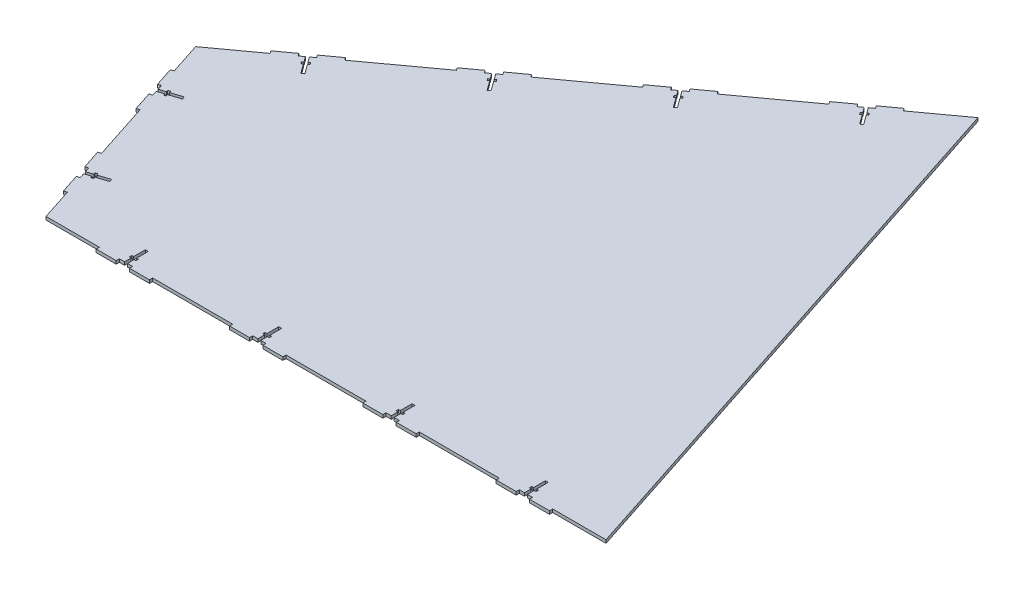
SolidWorks part; units mm, degrees
ref_plane "Front Plane" through (0, 0, 0) normal (0, 0, 1) x (1, 0, 0)
ref_plane "Top Plane" through (0, 0, 0) normal (0, 1, 0) x (1, 0, 0)
ref_plane "Right Plane" through (0, 0, 0) normal (1, 0, 0) x (0, 0, -1)
sketch "Sketch5" plane through (0, 0, 0) normal (0, 1, 0) x (1, 0, 0)
  line L0 (0, 0) -> (533.4, 0)
  line L1 (533.4, 0) -> (362.4036, 525.3201)
  line L2 (362.4036, 525.3201) -> (-68.7917, 211.3357)
  line L3 (-68.7917, 211.3357) -> (0, 0)
  line L4 (-68.7917, 211.3357) -> (413.506, 368.3279) construction
  line L5 (0, 0) -> (482.2976, 156.9922) construction
  dimension "D1" = 222.25
  dimension "D2" = 165.1
  dimension "D3" = 165.1
  dimension "D4" = 533.4
extrude "Boss-Extrude1" add sketch "Sketch5" along normal blind 3
sketch "Sketch6" plane through (0, 3, 0) normal (0, 1, 0) x (1, 0, 0)
  line L0 (74.8284, 0) -> (77.5716, 0)
  line L1 (76.2, 19.86) -> (76.2, 0) construction
  line L2 (204.5716, 19.86) -> (204.5716, 8.636)
  line L3 (201.8284, 19.86) -> (204.5716, 19.86)
  line L4 (201.8284, 8.636) -> (201.8284, 19.86)
  line L5 (299.6955, 479.6578) -> (301.913, 481.2726)
  line L6 (0, 0) -> (533.4, 0) construction
  line L7 (74.8284, 0) -> (74.8284, 6.35)
  line L8 (74.8284, 6.35) -> (73.0504, 6.35)
  line L9 (73.0504, 6.35) -> (73.0504, 8.636)
  line L10 (73.0504, 8.636) -> (74.8284, 8.636)
  line L11 (74.8284, 8.636) -> (74.8284, 19.86)
  line L12 (74.8284, 19.86) -> (77.5716, 19.86)
  line L13 (77.5716, 19.86) -> (77.5716, 8.636)
  line L14 (77.5716, 8.636) -> (79.3496, 8.636)
  line L15 (79.3496, 8.636) -> (79.3496, 6.35)
  line L16 (79.3496, 6.35) -> (77.5716, 6.35)
  line L17 (77.5716, 6.35) -> (77.5716, 0)
  line L18 (200.0504, 8.636) -> (201.8284, 8.636)
  line L19 (200.0504, 6.35) -> (200.0504, 8.636)
  line L20 (201.8284, 6.35) -> (200.0504, 6.35)
  line L21 (201.8284, 0) -> (201.8284, 6.35)
  line L22 (204.5716, 6.35) -> (204.5716, 0)
  line L23 (206.3496, 6.35) -> (204.5716, 6.35)
  line L24 (206.3496, 8.636) -> (206.3496, 6.35)
  line L25 (204.5716, 8.636) -> (206.3496, 8.636)
  line L26 (201.8284, 0) -> (204.5716, 0)
  line L27 (331.5716, 19.86) -> (331.5716, 8.636)
  line L28 (328.8284, 19.86) -> (331.5716, 19.86)
  line L29 (328.8284, 8.636) -> (328.8284, 19.86)
  line L30 (327.0504, 8.636) -> (328.8284, 8.636)
  line L31 (327.0504, 6.35) -> (327.0504, 8.636)
  line L32 (328.8284, 6.35) -> (327.0504, 6.35)
  line L33 (328.8284, 0) -> (328.8284, 6.35)
  line L34 (331.5716, 6.35) -> (331.5716, 0)
  line L35 (333.3496, 6.35) -> (331.5716, 6.35)
  line L36 (333.3496, 8.636) -> (333.3496, 6.35)
  line L37 (331.5716, 8.636) -> (333.3496, 8.636)
  line L38 (328.8284, 0) -> (331.5716, 0)
  line L39 (458.5716, 19.86) -> (458.5716, 8.636)
  line L40 (455.8284, 19.86) -> (458.5716, 19.86)
  line L41 (455.8284, 8.636) -> (455.8284, 19.86)
  line L42 (454.0504, 8.636) -> (455.8284, 8.636)
  line L43 (454.0504, 6.35) -> (454.0504, 8.636)
  line L44 (455.8284, 6.35) -> (454.0504, 6.35)
  line L45 (455.8284, 0) -> (455.8284, 6.35)
  line L46 (458.5716, 6.35) -> (458.5716, 0)
  line L47 (460.3496, 6.35) -> (458.5716, 6.35)
  line L48 (460.3496, 8.636) -> (460.3496, 6.35)
  line L49 (458.5716, 8.636) -> (460.3496, 8.636)
  line L50 (455.8284, 0) -> (458.5716, 0)
  line L51 (306.9966, 474.2913) -> (308.4339, 475.3379)
  line L52 (308.4339, 475.3379) -> (307.0883, 477.1859)
  line L53 (307.0883, 477.1859) -> (305.6509, 476.1393)
  line L54 (305.6509, 476.1393) -> (301.913, 481.2726)
  line L55 (299.6955, 479.6578) -> (303.4334, 474.5245)
  line L56 (303.4334, 474.5245) -> (301.9961, 473.4779)
  line L57 (301.9961, 473.4779) -> (303.3417, 471.6299)
  line L58 (303.3417, 471.6299) -> (304.779, 472.6766)
  line L59 (304.779, 472.6766) -> (311.386, 463.6032)
  line L60 (311.386, 463.6032) -> (313.6036, 465.218)
  line L61 (313.6036, 465.218) -> (306.9966, 474.2913)
  line L62 (197.0299, 404.8996) -> (199.2475, 406.5144)
  line L63 (204.3311, 399.5331) -> (205.7684, 400.5797)
  line L64 (205.7684, 400.5797) -> (204.4227, 402.4277)
  line L65 (204.4227, 402.4277) -> (202.9854, 401.3811)
  line L66 (202.9854, 401.3811) -> (199.2475, 406.5144)
  line L67 (197.0299, 404.8996) -> (200.7678, 399.7663)
  line L68 (200.7678, 399.7663) -> (199.3305, 398.7197)
  line L69 (199.3305, 398.7197) -> (200.6762, 396.8717)
  line L70 (200.6762, 396.8717) -> (202.1135, 397.9184)
  line L71 (202.1135, 397.9184) -> (208.7205, 388.845)
  line L72 (208.7205, 388.845) -> (210.938, 390.4598)
  line L73 (210.938, 390.4598) -> (204.3311, 399.5331)
  line L74 (94.3644, 330.1414) -> (96.582, 331.7562)
  line L75 (101.6655, 324.7749) -> (103.1028, 325.8215)
  line L76 (103.1028, 325.8215) -> (101.7572, 327.6695)
  line L77 (-34.3958, 105.6678) -> (447.9018, 262.6601) construction
  line L78 (101.7572, 327.6695) -> (100.3199, 326.6229)
  line L79 (100.3199, 326.6229) -> (96.582, 331.7562)
  line L80 (94.3644, 330.1414) -> (98.1023, 325.0081)
  line L81 (98.1023, 325.0081) -> (96.665, 323.9615)
  line L82 (96.665, 323.9615) -> (98.0106, 322.1135)
  line L83 (98.0106, 322.1135) -> (99.448, 323.1602)
  line L84 (-2.3456, 251.8647) -> (-6.0836, 256.998)
  line L85 (-0.9083, 252.9113) -> (-2.3456, 251.8647)
  line L86 (0.4373, 251.0633) -> (-0.9083, 252.9113)
  line L87 (-1, 250.0167) -> (0.4373, 251.0633)
  line L88 (5.607, 240.9434) -> (-1, 250.0167)
  line L89 (3.3894, 239.3286) -> (5.607, 240.9434)
  line L90 (-68.7917, 211.3357) -> (0, 0) construction
  line L91 (533.4, 0) -> (362.4036, 525.3201) construction
  line L92 (-3.2176, 248.402) -> (3.3894, 239.3286)
  line L93 (-4.6549, 247.3553) -> (-3.2176, 248.402)
  line L94 (-6.0005, 249.2033) -> (-4.6549, 247.3553)
  line L95 (-4.5632, 250.2499) -> (-6.0005, 249.2033)
  line L96 (-8.3011, 255.3832) -> (-4.5632, 250.2499)
  line L97 (99.448, 323.1602) -> (106.0549, 314.0868)
  line L98 (106.0549, 314.0868) -> (108.2725, 315.7016)
  line L99 (108.2725, 315.7016) -> (101.6655, 324.7749)
  line L100 (-8.3011, 255.3832) -> (-6.0836, 256.998)
  line L101 (1.1954, 60.4906) -> (-17.6893, 54.3435) construction
  line L102 (-50.6778, 155.688) -> (-51.5269, 158.2965)
  line L103 (-43.8654, 162.6602) -> (-46.0391, 161.9526)
  line L104 (-46.0391, 161.9526) -> (-45.4888, 160.2619)
  line L105 (-45.4888, 160.2619) -> (-51.5269, 158.2965)
  line L106 (-50.6778, 155.688) -> (-44.6397, 157.6535)
  line L107 (-44.6397, 157.6535) -> (-44.0893, 155.9628)
  line L108 (-41.9156, 156.6703) -> (-42.4659, 158.361)
  line L109 (-44.0893, 155.9628) -> (-41.9156, 156.6703)
  line L110 (-43.315, 160.9695) -> (-43.8654, 162.6602)
  line L111 (-32.6422, 164.4436) -> (-43.315, 160.9695)
  line L112 (-31.7931, 161.8351) -> (-32.6422, 164.4436)
  line L113 (-42.4659, 158.361) -> (-31.7931, 161.8351)
  line L173 (-9.9019, 58.3208) -> (0.7709, 61.7948)
  line L174 (0.7709, 61.7948) -> (1.62, 59.1864)
  line L175 (1.62, 59.1864) -> (-9.0528, 55.7123)
  line L176 (-9.0528, 55.7123) -> (-8.5025, 54.0216)
  line L177 (-12.626, 59.3039) -> (-10.4523, 60.0114)
  line L178 (-10.4523, 60.0114) -> (-9.9019, 58.3208)
  line L179 (-12.0757, 57.6132) -> (-12.626, 59.3039)
  line L180 (-18.1138, 55.6477) -> (-12.0757, 57.6132)
  line L181 (-11.2266, 55.0047) -> (-17.2647, 53.0392)
  line L182 (-10.6762, 53.314) -> (-11.2266, 55.0047)
  line L183 (-8.5025, 54.0216) -> (-10.6762, 53.314)
  line L184 (-18.1138, 55.6477) -> (-17.2647, 53.0392)
  dimension "D3" = 11.224
  dimension "D4" = 2.7432
  dimension "D5" = 6.2992
  dimension "D6" = 2.286
  dimension "D7" = 76.2
  dimension "D8" = 19.86
  dimension "D9" = 6.35
  dimension "D10" = 4
  dimension "D15" = 2.7432
  dimension "D16" = 6.2992
  dimension "D27" = 2.286
  dimension "D28" = 6.35
  dimension "D11" = 57.15
extrude "Cut-Extrude1" cut sketch "Sketch6" against normal through all
sketch "Sketch8" plane through (0, 0, 0) normal (0, 1, 0) x (1, 0, 0)
  line L0 (-15.7238, 48.3053) -> (-18.5765, 47.3767)
  line L1 (-17.2647, 53.0392) -> (0, 0) construction
  line L2 (-18.5765, 47.3767) -> (-12.6801, 29.2622)
  line L3 (-12.6801, 29.2622) -> (-9.8274, 30.1908)
  line L4 (-15.7238, 48.3053) -> (-9.8274, 30.1908)
  line L5 (-32.2177, 163.1394) -> (-52.5287, 156.5279) construction
  line L6 (-25.5512, 78.4961) -> (-28.4039, 77.5675)
  line L7 (-28.4039, 77.5675) -> (-22.5074, 59.4531)
  line L8 (-22.5074, 59.4531) -> (-19.6548, 60.3816)
  line L9 (-25.5512, 78.4961) -> (-19.6548, 60.3816)
  line L11 (-50.6778, 155.688) -> (-18.1138, 55.6477) construction
  line L12 (-21.0811, 59.9173) -> (-17.1501, 47.841) construction
  line L13 (-17.1501, 47.841) -> (-19.1156, 53.8792) construction
  line L14 (-19.1156, 53.8792) -> (1.1954, 60.4906) construction
  line L15 (1.62, 59.1864) -> (0.7709, 61.7948) construction
  line L16 (0.7709, 61.7948) -> (-9.9019, 58.3208) construction
  line L17 (-58.9643, 181.1449) -> (-61.817, 180.2163)
  line L18 (-61.817, 180.2163) -> (-55.9205, 162.1018)
  line L19 (-55.9205, 162.1018) -> (-53.0679, 163.0304)
  line L20 (-58.9643, 181.1449) -> (-53.0679, 163.0304)
  line L21 (-49.1369, 150.9541) -> (-51.9896, 150.0255)
  line L22 (-51.9896, 150.0255) -> (-46.0932, 131.911)
  line L23 (-46.0932, 131.911) -> (-43.2405, 132.8396)
  line L24 (-49.1369, 150.9541) -> (-43.2405, 132.8396)
  line L25 (-31.7931, 161.8351) -> (-32.6422, 164.4436) construction
  line L26 (-54.4942, 162.5661) -> (-50.5632, 150.4898) construction
  line L27 (-32.6422, 164.4436) -> (-43.315, 160.9695) construction
  point P30 (-50.5632, 150.4898)
  dimension "D1" = 3
  dimension "D2" = 19.05
  dimension "D3" = 12.7
  dimension "D4" = 19.05
  dimension "D5" = 3
  dimension "D6" = 19.05
  dimension "D7" = 3
  dimension "D8" = 19.05
  dimension "D9" = 12.7
extrude "Boss-Extrude2" add sketch "Sketch8" along normal blind 3
sketch "Sketch9" plane through (0, 0, 0) normal (0, 1, 0) x (1, 0, 0)
  line L0 (0, 0) -> (74.8284, 0) construction
  line L1 (50.8, 0) -> (69.85, 0)
  line L2 (50.8, 0) -> (50.8, -3)
  line L3 (50.8, -3) -> (69.85, -3)
  line L4 (69.85, 0) -> (69.85, -3)
  line L5 (77.5716, 0) -> (201.8284, 0) construction
  line L6 (69.85, -1.5) -> (82.55, -1.5) construction
  line L7 (82.55, 0) -> (101.6, 0)
  line L8 (82.55, 0) -> (82.55, -3)
  line L9 (82.55, -3) -> (101.6, -3)
  line L10 (101.6, 0) -> (101.6, -3)
  line L11 (76.2, -1.5) -> (76.2, 19.86) construction
  line L12 (77.5716, 19.86) -> (74.8284, 19.86) construction
  line L13 (74.8284, 19.86) -> (74.8284, 8.636) construction
  line L14 (177.8, -3) -> (196.85, -3)
  line L15 (177.8, 0) -> (177.8, -3)
  line L16 (177.8, 0) -> (196.85, 0)
  line L17 (196.85, 0) -> (196.85, -3)
  line L18 (209.55, 0) -> (209.55, -3)
  line L19 (209.55, 0) -> (228.6, 0)
  line L20 (209.55, -3) -> (228.6, -3)
  line L21 (228.6, 0) -> (228.6, -3)
  line L22 (304.8, -3) -> (323.85, -3)
  line L23 (304.8, 0) -> (304.8, -3)
  line L24 (304.8, 0) -> (323.85, 0)
  line L25 (323.85, 0) -> (323.85, -3)
  line L26 (336.55, 0) -> (336.55, -3)
  line L27 (336.55, 0) -> (355.6, 0)
  line L28 (336.55, -3) -> (355.6, -3)
  line L29 (355.6, 0) -> (355.6, -3)
  line L30 (431.8, -3) -> (450.85, -3)
  line L31 (431.8, 0) -> (431.8, -3)
  line L32 (431.8, 0) -> (450.85, 0)
  line L33 (450.85, 0) -> (450.85, -3)
  line L34 (463.55, 0) -> (463.55, -3)
  line L35 (463.55, 0) -> (482.6, 0)
  line L36 (463.55, -3) -> (482.6, -3)
  line L37 (482.6, 0) -> (482.6, -3)
  line L38 (-34.3958, 105.6678) -> (447.9018, 262.6601) construction
  line L39 (-43.2405, 132.8396) -> (-25.5512, 78.4961) construction
  line L40 (533.4, 0) -> (362.4036, 525.3201) construction
  line L41 (321.3374, 495.4168) -> (319.5714, 497.842)
  line L42 (304.1716, 486.6283) -> (319.5714, 497.842)
  line L43 (305.9375, 484.2031) -> (321.3374, 495.4168)
  line L44 (305.9375, 484.2031) -> (304.1716, 486.6283)
  line L45 (295.671, 476.7273) -> (293.905, 479.1525)
  line L46 (280.2711, 465.5136) -> (295.671, 476.7273)
  line L47 (280.2711, 465.5136) -> (278.5052, 467.9387)
  line L48 (278.5052, 467.9387) -> (293.905, 479.1525)
  line L49 (218.6718, 420.6586) -> (216.9059, 423.0838)
  line L50 (201.5061, 411.8701) -> (216.9059, 423.0838)
  line L51 (203.272, 409.4449) -> (218.6718, 420.6586)
  line L52 (203.272, 409.4449) -> (201.5061, 411.8701)
  line L53 (193.0054, 401.9691) -> (191.2395, 404.3943)
  line L54 (177.6056, 390.7554) -> (193.0054, 401.9691)
  line L55 (177.6056, 390.7554) -> (175.8397, 393.1805)
  line L56 (175.8397, 393.1805) -> (191.2395, 404.3943)
  line L57 (116.0063, 345.9004) -> (114.2404, 348.3256)
  line L58 (98.8405, 337.1119) -> (114.2404, 348.3256)
  line L59 (100.6065, 334.6867) -> (116.0063, 345.9004)
  line L60 (100.6065, 334.6867) -> (98.8405, 337.1119)
  line L61 (90.3399, 327.2109) -> (88.574, 329.6361)
  line L62 (74.9401, 315.9972) -> (90.3399, 327.2109)
  line L63 (74.9401, 315.9972) -> (73.1741, 318.4223)
  line L64 (73.1741, 318.4223) -> (88.574, 329.6361)
  line L65 (13.3408, 271.1422) -> (11.5748, 273.5674)
  line L66 (-3.825, 262.3537) -> (11.5748, 273.5674)
  line L67 (-2.0591, 259.9285) -> (-3.825, 262.3537)
  line L68 (-2.0591, 259.9285) -> (13.3408, 271.1422)
  line L69 (-12.3256, 252.4527) -> (-14.0916, 254.8779)
  line L70 (-29.4914, 243.6641) -> (-14.0916, 254.8779)
  line L71 (-27.7255, 241.239) -> (-29.4914, 243.6641)
  line L72 (-27.7255, 241.239) -> (-12.3256, 252.4527)
  point P20 (82.55, -1.5)
  dimension "D1" = 3
  dimension "D2" = 3
  dimension "D3" = 19.05
  dimension "D4" = 19.05
  dimension "D5" = 12.7
  dimension "D6" = 4
extrude "Boss-Extrude3" add sketch "Sketch9" along normal blind 3
